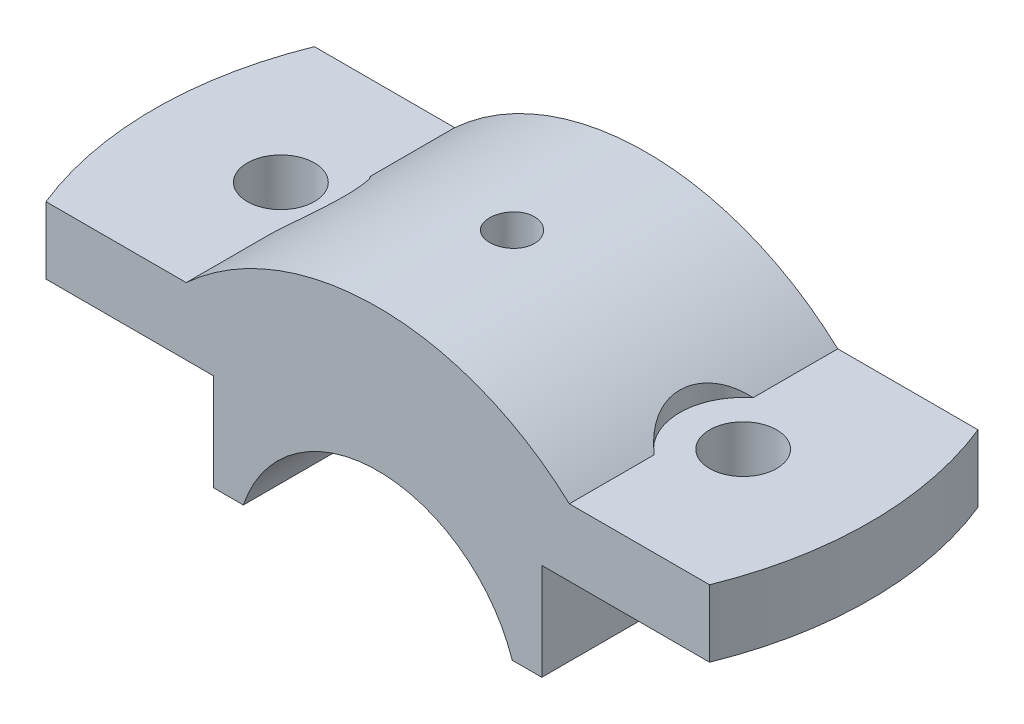
SolidWorks part; units mm, degrees
ref_plane "Front Plane" through (0, 0, 0) normal (0, 0, 1) x (1, 0, 0)
ref_plane "Top Plane" through (0, 0, 0) normal (0, 1, 0) x (1, 0, 0)
ref_plane "Right Plane" through (0, 0, 0) normal (1, 0, 0) x (0, 0, -1)
sketch "Sketch1" plane through (0, 0, 0) normal (0, 0, 1) x (1, 0, 0)
  line L0 (0, 0) -> (0, 1386.224) construction
  line L1 (457.905, 152.4) -> (558.8, 152.4)
  line L2 (558.8, 152.4) -> (558.8, 482.6)
  line L3 (558.8, 482.6) -> (1270, 482.6)
  line L4 (1270, 482.6) -> (1270, 711.2)
  line L5 (1270, 711.2) -> (652.5378, 711.2)
  line L6 (-457.905, 152.4) -> (-558.8, 152.4)
  line L7 (-558.8, 152.4) -> (-558.8, 482.6)
  line L8 (-558.8, 482.6) -> (-1270, 482.6)
  line L9 (-1270, 482.6) -> (-1270, 711.2)
  line L10 (-1270, 711.2) -> (-652.5378, 711.2)
  arc A0 (-457.905, 152.4) -> (457.905, 152.4) centre (0, 0) cw
  arc A1 (-652.5378, 711.2) -> (652.5378, 711.2) centre (0, 0) cw
  dimension "D2" = 482.6
  dimension "D3" = 965.2
  dimension "D1" = 1117.6
  dimension "D4" = 152.4
  dimension "D5" = 330.2
  dimension "D6" = 228.6
  dimension "D7" = 1270
extrude "Boss-Extrude1" add sketch "Sketch1" along normal mid plane 914.4
sketch "Sketch2" plane through (0, 0, 457.2) normal (0, 0, 1) x (1, 0, 0)
  circle A1 centre (-955.2202, 600.328) radius 14.0593
hole_wizard "#97 (0.0059) Diameter Hole1" positions "Sketch4" profile "Sketch3" hole size "#97" standard "ANSI Inch" end condition up to next
sketch "Sketch4" plane through (0, 711.2, 0) normal (0, 1, 0) x (1, 0, 0)
  point P0 (-787.4, 0)
  dimension "D1" = 787.4
  dimension "D2" = 0
sketch "Sketch3" plane through (-787.4, 711.2, 0) normal (1, 0, 0) x (0, 0, 1)
  line L0 (0, 0) -> (0, 228.601)
  line L1 (0, 228.601) -> (114.3, 228.601)
  line L2 (114.3, 228.601) -> (114.3, 0)
  line L5 (114.3, 0) -> (0, 0)
  line L11 (0, -6.35) -> (0, 107.95) construction
  dimension "Thru Hole Dia." = 228.6
  dimension "Thru Hole Depth" = 228.601
mirror "Mirror7" about plane through (0, 0, 0) normal (1, 0, 0) of "#97 (0.0059) Diameter Hole1"
sketch "Sketch5" plane through (0, 711.2, 0) normal (0, 1, 0) x (1, 0, 0)
  line L0 (-652.5378, -457.2) -> (-652.5378, 457.2) construction
  line L1 (-652.5378, 168.5972) -> (-652.5378, -168.5972)
  arc A0 (-652.5378, 168.5972) -> (-652.5378, -168.5972) centre (-787.4, 0) cw
  dimension "D1" = 215.9
extrude "Cut-Extrude1" cut sketch "Sketch5" along normal up to next contours A0 L1
mirror "Mirror8" about plane through (0, 0, 0) normal (1, 0, 0) of "Cut-Extrude1"
sketch "Sketch6" plane through (0, 711.2, 0) normal (0, 1, 0) x (1, 0, 0)
  line L0 (-1130.2286, 457.2) -> (-1270, 457.2)
  line L1 (-652.5378, 457.2) -> (-1270, 457.2) construction
  line L2 (-1270, 457.2) -> (-1270, -457.2)
  line L3 (-1270, -457.2) -> (-1130.2286, -457.2)
  line L6 (1130.2286, 457.2) -> (1270, 457.2)
  line L7 (1270, 457.2) -> (652.5378, 457.2) construction
  line L8 (1270, 457.2) -> (1270, -457.2)
  line L9 (1270, -457.2) -> (1130.2286, -457.2)
  line L10 (1270, -457.2) -> (652.5378, -457.2) construction
  arc A0 (-1130.2286, 457.2) -> (-1130.2286, -457.2) centre (0, 0) ccw
  arc A1 (1130.2286, -457.2) -> (1130.2286, 457.2) centre (0, 0) ccw
  dimension "D1" = 1219.2
extrude "Cut-Extrude2" cut sketch "Sketch6" against normal up to next contours A1 L6 L8 L9 | A0 L3 L2 L0
hole_wizard "CSK for M10 Flat Head Machine Screw1" positions "3DSketch2" profile "Sketch10" countersink size "M10" standard "ANSI Metric"
sketch3d "3DSketch2"
  point P0 (0, 965.2, 0)
  dimension "D1" = 0
  dimension "D2" = 0
sketch "Sketch10" plane through (0, 965.2, 0) normal (1, 0, 0) x (0, 0, 1)
  line L0 (0, 0) -> (0, 3060.7546)
  line L1 (0, 3060.7546) -> (63.5, 3022.6)
  line L2 (63.5, 3022.6) -> (63.5, 342.9)
  line L3 (63.5, 342.9) -> (76.2, 330.2)
  line L4 (76.2, 330.2) -> (76.2, 0)
  line L6 (76.2, 0) -> (0, 0)
  line L7 (-63.5, 342.9) -> (-76.2, 330.2) construction
  line L10 (0, 3060.7546) -> (-63.5, 3022.6) construction
  line L11 (0, -6.35) -> (0, 107.95) construction
  dimension "Hole Dia." = 127
  dimension "Hole Depth" = 3022.6
  dimension "C'Sink Dia." = 152.4
  dimension "C'Sink Angle" = 90
  dimension "Drill Angle" = 118
  dimension "Head Clearance" = 330.2
